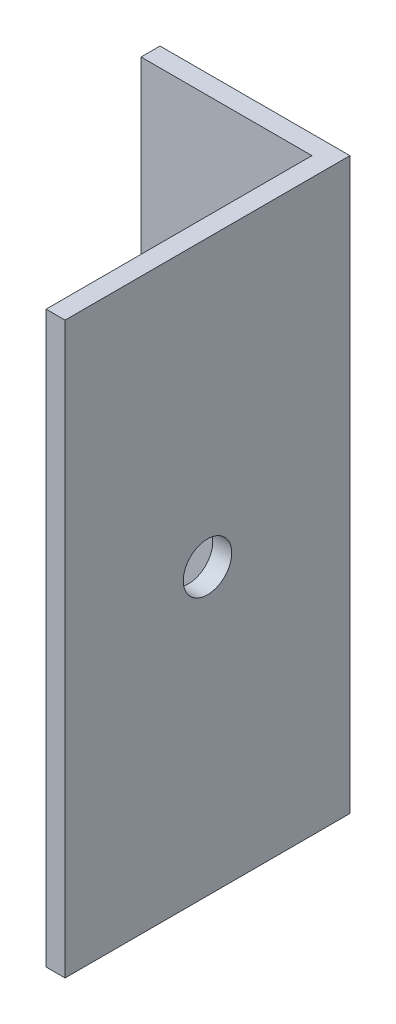
SolidWorks part; units mm, degrees
ref_plane "Front" through (0, 0, 0) normal (0, 0, 1) x (1, 0, 0)
ref_plane "Top" through (0, 0, 0) normal (0, 1, 0) x (1, 0, 0)
ref_plane "Right" through (0, 0, 0) normal (1, 0, 0) x (0, 0, -1)
sketch "Sketch1" plane through (0, 0, 0) normal (0, 1, 0) x (1, 0, 0)
  line L0 (-9.2362, 0) -> (10.7638, 0)
  line L1 (10.7638, 0) -> (10.7638, -30)
  line L2 (10.7638, -30) -> (8.7638, -30)
  line L3 (8.7638, -30) -> (8.7638, -2)
  line L4 (8.7638, -2) -> (-9.2362, -2)
  line L5 (-9.2362, -2) -> (-9.2362, 0)
  dimension "D1" = 20
  dimension "D2" = 30
  dimension "D3" = 2
  dimension "D4" = 2
extrude "Boss-Extrude1" add sketch "Sketch1" along normal blind 60
sketch "Sketch2" plane through (10.7638, 0, 0) normal (1, 0, 0) x (0, 0, -1)
  circle A0 centre (-15, 30) radius 2.55
extrude "Cut-Extrude1" cut sketch "Sketch2" against normal blind 60
